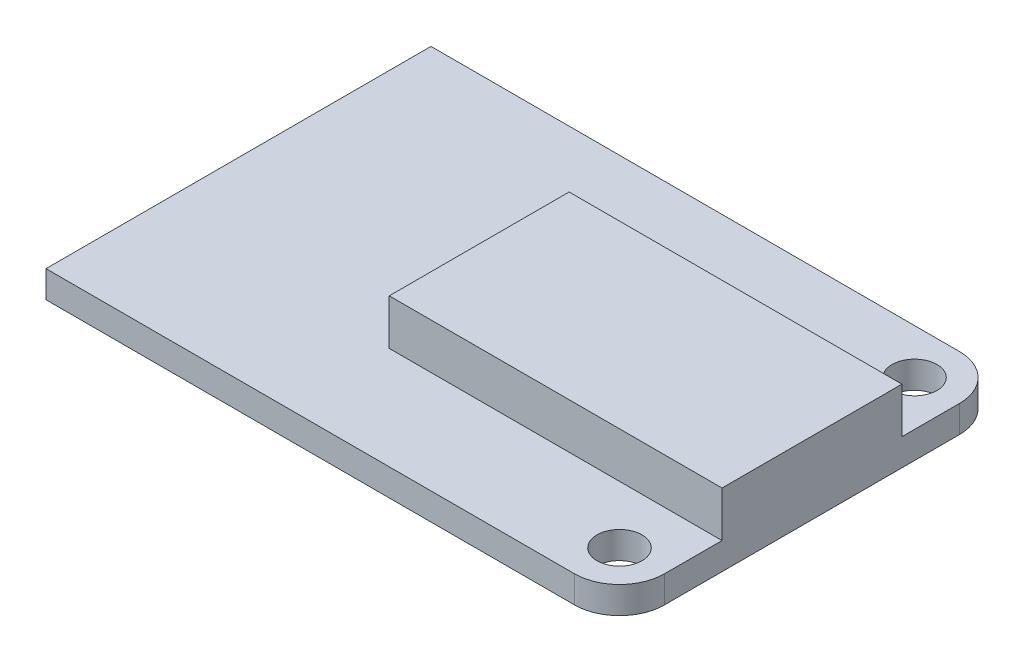
SolidWorks part; units mm, degrees
ref_plane "Front Plane" through (0, 0, 0) normal (0, 0, 1) x (1, 0, 0)
ref_plane "Top Plane" through (0, 0, 0) normal (0, 1, 0) x (1, 0, 0)
ref_plane "Right Plane" through (0, 0, 0) normal (1, 0, 0) x (0, 0, -1)
sketch "Sketch1" plane through (0, 0, 0) normal (0, 1, 0) x (1, 0, 0)
  line L1 (0, 0) -> (29.38, 0)
  line L2 (0, 0) -> (0, 21.4)
  line L3 (0, 21.4) -> (29.38, 21.4)
  line L4 (31.88, 2.5) -> (31.88, 18.9)
  arc A0 (31.88, 2.5) -> (29.38, 0) centre (29.38, 2.5) cw
  arc A1 (31.88, 18.9) -> (29.38, 21.4) centre (29.38, 18.9) ccw
  circle A2 centre (29.38, 18.9) radius 1.25
  circle A3 centre (29.38, 2.5) radius 1.25
  point P7 (31.88, 0)
  dimension "D3" = 2.5
  dimension "D4" = 2.5
  dimension "D1" = 31.88
  dimension "D2" = 21.4
extrude "Boss-Extrude1" add sketch "Sketch1" along normal blind 1.5 contours L4 A1 L3 L2 L1 A0 A3 A2
sketch "Sketch3" plane through (0, 1.5, 0) normal (0, 1, 0) x (1, 0, 0)
  line L1 (13.38, 15.7) -> (31.88, 15.7)
  line L2 (13.38, 15.7) -> (13.38, 5.7)
  line L3 (13.38, 5.7) -> (31.88, 5.7)
  line L4 (31.88, 15.7) -> (31.88, 5.7)
  line L5 (31.88, 2.5) -> (31.88, 18.9) construction
  line L7 (0, 10.7) -> (13.38, 10.7) construction
  line L8 (0, 0) -> (0, 21.4) construction
  point P4 (13.38, 15.7)
  dimension "D1" = 10
  dimension "D2" = 18.5
extrude "Boss-Extrude2" add sketch "Sketch3" along normal blind 2.53
